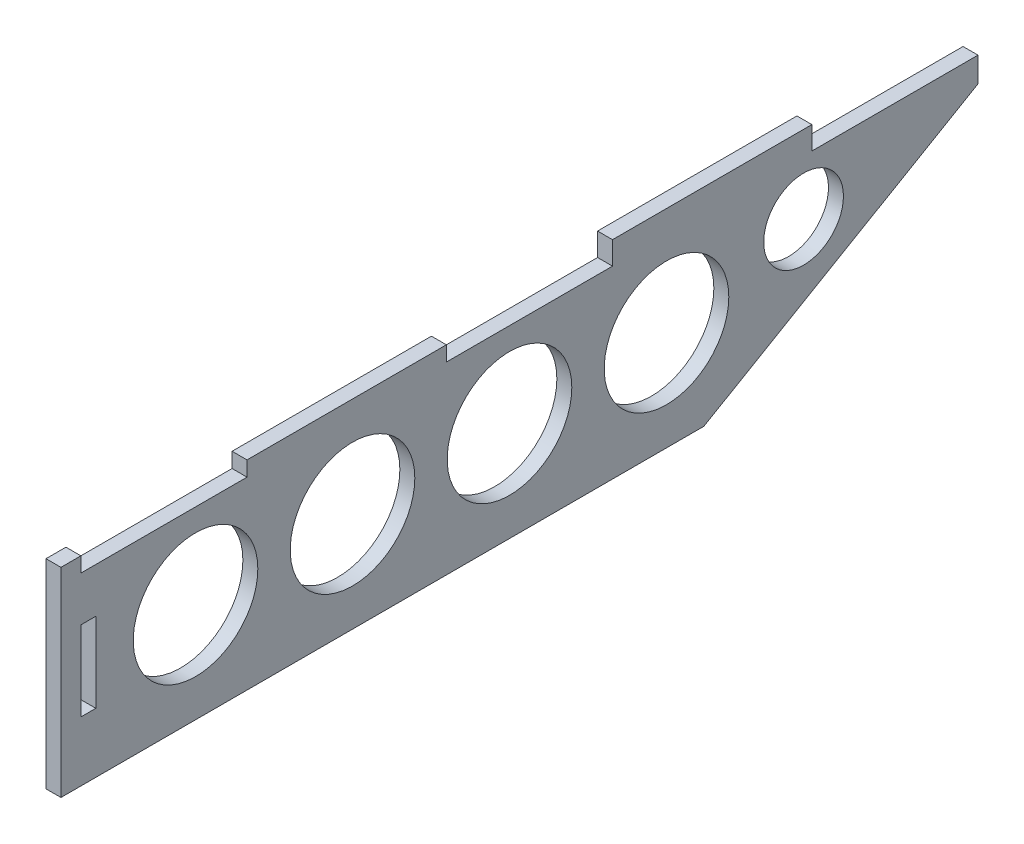
SolidWorks part; units mm, degrees
ref_plane "Front Plane" through (0, 0, 0) normal (0, 0, 1) x (1, 0, 0)
ref_plane "Top Plane" through (0, 0, 0) normal (0, 1, 0) x (1, 0, 0)
ref_plane "Right Plane" through (0, 0, 0) normal (1, 0, 0) x (0, 0, -1)
sketch "Sketch1" plane through (0, 0, 0) normal (1, 0, 0) x (0, 0, -1)
  line L0 (180, -8) -> (125, -40)
  line L1 (0, 0) -> (180, 0)
  line L2 (0, 0) -> (0, -40) construction
  line L3 (0, -40) -> (125, -40)
  line L4 (180, 0) -> (180, -8)
  line L5 (125, -40) -> (180, -40) construction
  line L6 (180, -8) -> (180, -40) construction
  line L7 (0, -20) -> (180, -20) construction
  line L8 (0, 0) -> (33.3333, 0)
  line L9 (0, 0) -> (0, -3)
  line L10 (0, -3) -> (33.3333, -3)
  line L11 (33.3333, 0) -> (33.3333, -3)
  line L12 (73.3333, 0) -> (106.6667, 0)
  line L13 (73.3333, 0) -> (73.3333, -3)
  line L14 (73.3333, -3) -> (106.6667, -3)
  line L15 (106.6667, 0) -> (106.6667, -3)
  line L16 (146.6667, 0) -> (180, 0)
  line L17 (146.6667, 0) -> (146.6667, -3)
  line L18 (146.6667, -3) -> (180, -3)
  line L19 (180, 0) -> (180, -3)
  line L20 (0, -12) -> (3, -12)
  line L21 (0, -12) -> (0, -28)
  line L22 (0, -28) -> (3, -28)
  line L23 (3, -12) -> (3, -28)
  line L24 (0, -40) -> (-4, -40)
  line L25 (-4, -40) -> (-4, 0)
  line L26 (-4, 0) -> (0, 0)
  circle A0 centre (23, -20) radius 12.5
  circle A1 centre (54.5, -20) radius 12.5
  circle A2 centre (86, -20) radius 12.5
  circle A3 centre (117.5, -20) radius 12.5
  circle A4 centre (145, -14) radius 8
  dimension "D12" = 25
  dimension "D13" = 16
  dimension "D1" = 40
  dimension "D2" = 180
  dimension "D3" = 8
  dimension "D4" = 125
  dimension "D5" = 3
  dimension "D10" = 9
  dimension "D11" = 16
  dimension "D14" = 145
  dimension "D15" = 14
  dimension "D16" = 23
  dimension "D17" = 31.5
  dimension "D18" = 31.5
  dimension "D19" = 31.5
  dimension "D7" = 40
  dimension "D6" = 40
  dimension "D8" = 4
extrude "Boss-Extrude1" add sketch "Sketch1" along normal blind 3 contours L20 L23 L22 L2 L3 L0 L4 L18 L17 L1 L15 L14 L13 L11 L10 A4 A3 A2 A1 A0
sketch "Sketch2" plane through (3, 0, 0) normal (1, 0, 0) x (0, 0, -1)
  line L0 (146.6667, 0) -> (146.6667, -3) construction
  line L1 (106.6667, 0) -> (146.6667, 0)
  line L2 (106.6667, 0) -> (106.6667, 1.6)
  line L3 (106.6667, 1.6) -> (146.6667, 1.6)
  line L4 (146.6667, 0) -> (146.6667, 1.6)
  dimension "D1" = 1.6
extrude "Boss-Extrude2" add sketch "Sketch2" against normal blind 3
equation "\"D18@Sketch1\"=\"D19@Sketch1\""
equation "\"D17@Sketch1\"=\"D19@Sketch1\""
